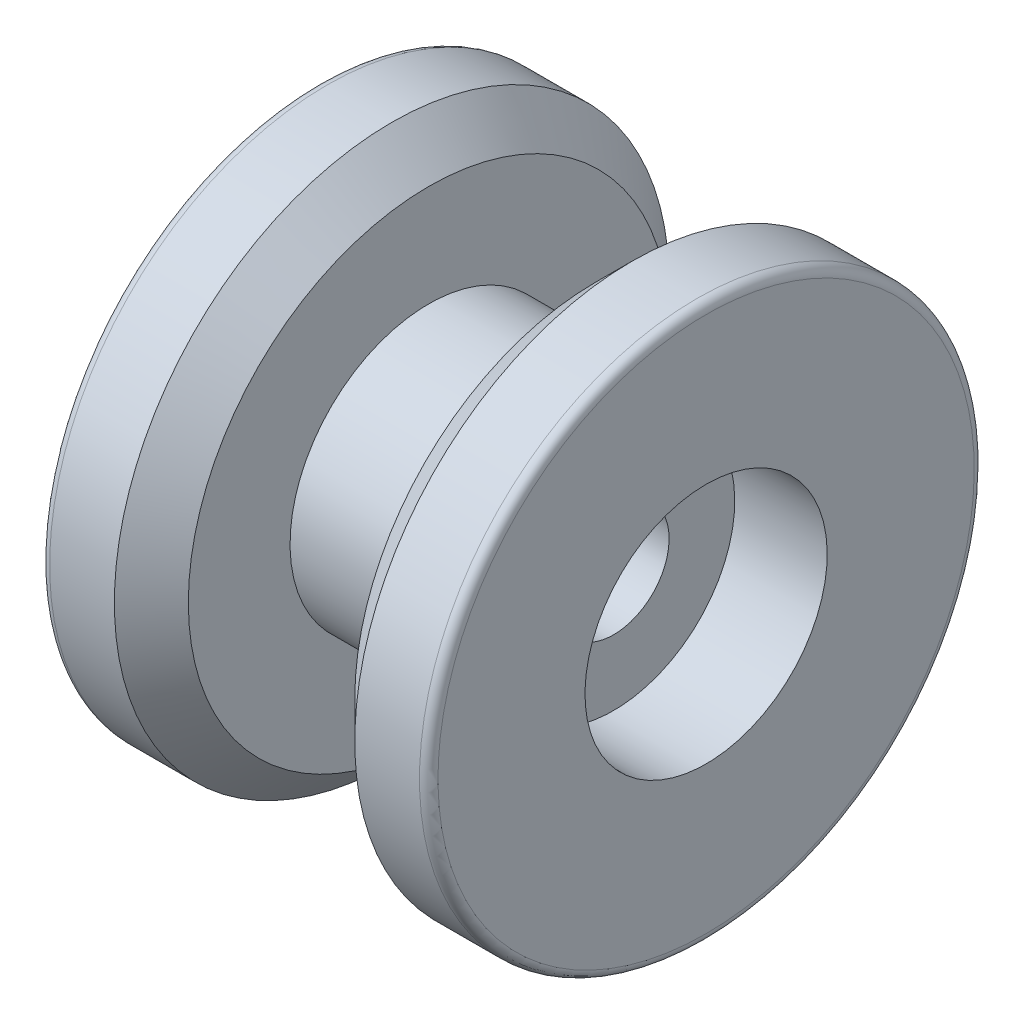
SolidWorks part; units mm, degrees
ref_plane "Front Plane" through (0, 0, 0) normal (0, 0, 1) x (1, 0, 0)
ref_plane "Top Plane" through (0, 0, 0) normal (0, 1, 0) x (1, 0, 0)
ref_plane "Right Plane" through (0, 0, 0) normal (1, 0, 0) x (0, 0, -1)
sketch "Sketch1" plane through (0, 0, 0) normal (0, 0, 1) x (1, 0, 0)
  line L0 (-21, 0) -> (21, 0)
  line L1 (21, 0) -> (21, 30)
  line L2 (21, 30) -> (9, 30)
  line L3 (9, 30) -> (9, 15)
  line L4 (9, 15) -> (-9, 15)
  line L5 (-9, 15) -> (-9, 30)
  line L6 (-9, 30) -> (-21, 30)
  line L7 (-21, 30) -> (-21, 0)
  point P10 (0, 0)
  point P13 (0, 15)
  dimension "D1" = 12
  dimension "D2" = 18
  dimension "D3" = 30
  dimension "D4" = 15
revolve "Revolve1" add sketch "Sketch1" angle 360 about L0
fillet "Fillet1" [suppressed] radius 4
fillet "Fillet2" [suppressed] radius 2
sketch "Sketch2" plane through (21, 0, 0) normal (1, 0, 0) x (0, 0, -1)
  circle A0 centre (0, 0) radius 9
  dimension "D1" = 18
extrude "Boss-Extrude1" add sketch "Sketch2" along normal blind 10
fillet "Fillet3" [suppressed] radius 3
sketch "Sketch3" plane through (31, 0, 0) normal (1, 0, 0) x (0, 0, -1)
  circle A0 centre (0, 0) radius 6
  circle A1 centre (0, 0) radius 30 construction
  dimension "D1" = 12
extrude "Cut-Extrude1" cut sketch "Sketch3" against normal through all
hole_wizard "Ø1.0mm Dowel Hole1" [suppressed] positions "3DSketch1" profile "Sketch4" hole size "Ø1.0" standard "ANSI Metric"
sketch3d "3DSketch1" [suppressed]
  point P0 (24.1787, 8.421, 3.1759)
  point P2 (24.3919, 1.4216, -8.887)
sketch "Sketch4" plane through (24.1787, 8.421, 3.1759) normal (1, 0, 0) x (0, -0.3529, 0.9357)
  line L0 (0, 0) -> (0, 34)
  line L1 (0, 34) -> (1.4, 33.1588)
  line L2 (1.4, 33.1588) -> (1.4, 0)
  line L5 (1.4, 0) -> (0, 0)
  line L10 (0, 34) -> (-1.4, 33.1588) construction
  line L11 (0, -6.35) -> (0, 107.95) construction
  dimension "Hole Dia." = 2.8
  dimension "Hole Depth" = 34
  dimension "Drill Angle" = 118
chamfer "Chamfer1" distance 4 angle 45 2 edges at (9, -30, 0) (-9, -30, 0)
fillet "Fillet4" radius 1 2 edges at (21, -30, 0) (-21, -30, 0)
sketch "Sketch5" plane through (0, 0, 0) normal (0, 0, 1) x (1, 0, 0)
  line L1 (8.9, -29.0567) -> (9, -29.0567)
  line L2 (8.9, -29.0567) -> (8.9, 25.4884)
  line L3 (8.9, 25.4884) -> (9, 25.4884)
  line L4 (9, -29.0567) -> (9, 25.4884)
  dimension "D1" = 0.1
extrude "Cut-Extrude2" [suppressed] cut sketch "Sketch5" against normal through all both and the other way through all
sketch "Sketch6" plane through (21, 0, 0) normal (1, 0, 0) x (0, 0, -1)
  circle A0 centre (0, 0) radius 15 construction
  circle A1 centre (0, 0) radius 15
  point P4 (0, 10)
  point P7 (10, 0)
  point P8 (0, -10)
  point P9 (-10, 0)
  point P10 (0, 0)
  dimension "D1" = 10
  dimension "D2" = 4
hole_wizard "Ø1.0mm Dowel Hole2" [suppressed] positions "3DSketch2" profile "Sketch7" hole size "Ø1.0" standard "ANSI Metric"
sketch3d "3DSketch2"
  point P8 (0, 0, 0)
  point P9 (0, 0, 0)
  point P10 (0, 0, 0)
  point P11 (0, 0, 0)
  point P12 (19, -10, 0)
  point P14 (19, 0, 10)
  point P16 (19, 10, 0)
  point P18 (19, 0, -10)
sketch "Sketch7" plane through (19, -10, 0) normal (0, 1, 0) x (0, 0, -1)
  line L0 (0, 0) -> (0, 50)
  line L1 (0, 50) -> (1.45, 49.1288)
  line L2 (1.45, 49.1288) -> (1.45, 0)
  line L5 (1.45, 0) -> (0, 0)
  line L10 (0, 50) -> (-1.45, 49.1288) construction
  line L11 (0, -6.35) -> (0, 107.95) construction
  dimension "Hole Dia." = 2.9
  dimension "Hole Depth" = 50
  dimension "Drill Angle" = 118
sketch "Sketch8" plane through (0, 0, 0) normal (0, 1, 0) x (1, 0, 0)
  line L0 (21, -29) -> (21, 29) construction
  line L1 (31, 11.0653) -> (21, 11.0653)
  line L2 (31, 11.0653) -> (31, -10.1114)
  line L3 (31, -10.1114) -> (21, -10.1114)
  line L4 (21, 11.0653) -> (21, -10.1114)
  point P6 (29, -9)
  point P8 (29, -10.1114)
  dimension "D1" = 10
extrude "Cut-Extrude3" cut sketch "Sketch8" against normal through all both and the other way through all
sketch "Sketch9" [suppressed] plane through (8.9, 0, 0) normal (1, 0, 0) x (0, 0, -1)
  circle A0 centre (0, 0) radius 12.7024
sketch "Sketch10" plane through (21, 0, 0) normal (1, 0, 0) x (0, 0, -1)
  circle A0 centre (0, 0) radius 13.1
  point P2 (0, 0)
  dimension "D1" = 26.2
extrude "Cut-Extrude4" cut sketch "Sketch10" against normal blind 10
